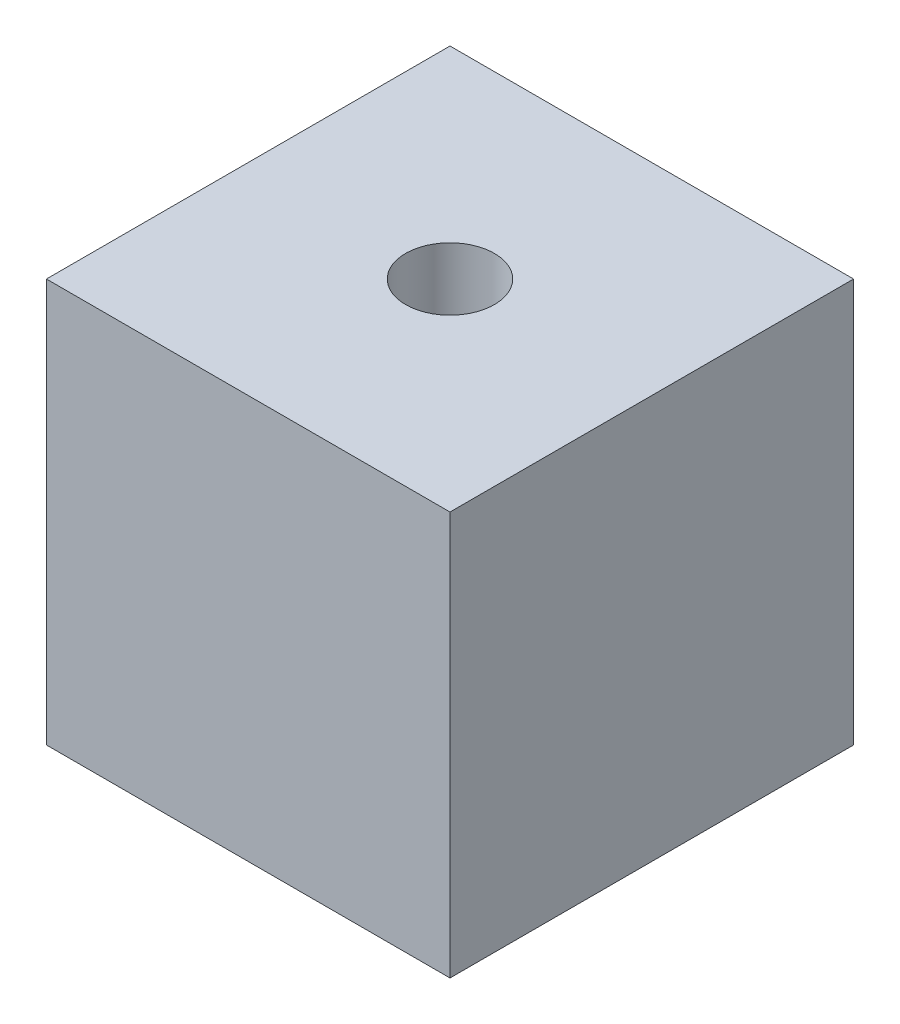
SolidWorks part; units mm, degrees
ref_plane "Front Plane" through (0, 0, 0) normal (0, 0, 1) x (1, 0, 0)
ref_plane "Top Plane" through (0, 0, 0) normal (0, 1, 0) x (1, 0, 0)
ref_plane "Right Plane" through (0, 0, 0) normal (1, 0, 0) x (0, 0, -1)
sketch "Sketch1" plane through (0, 0, 0) normal (0, 1, 0) x (1, 0, 0)
  line L1 (0, 0) -> (10, 0)
  line L2 (0, 0) -> (0, 10)
  line L3 (0, 10) -> (10, 10)
  line L4 (10, 0) -> (10, 10)
  dimension "D1" = 10
  dimension "D2" = 10
extrude "Boss-Extrude1" add sketch "Sketch1" along normal blind 10
hole_wizard "M2 Clearance Hole1" positions "Sketch2" profile "Sketch3" hole size "M2" standard "ISO"
sketch "Sketch2" plane through (0, 10, 0) normal (0, 1, 0) x (1, 0, 0)
  line L0 (10, 10) -> (0, 10) construction
  line L1 (10, 0) -> (10, 10) construction
  point P0 (5, 5)
  dimension "D1" = 5
  dimension "D2" = 5
sketch "Sketch3" plane through (5, 10, -5) normal (1, 0, 0) x (0, 0, 1)
  line L0 (0, 0) -> (0, 8)
  line L1 (0, 8) -> (1.1, 7.3391)
  line L2 (1.1, 7.3391) -> (1.1, 0)
  line L5 (1.1, 0) -> (0, 0)
  line L10 (0, 8) -> (-1.1, 7.3391) construction
  line L11 (0, -6.35) -> (0, 107.95) construction
  dimension "Hole Dia." = 2.2
  dimension "Hole Depth" = 8
  dimension "Drill Angle" = 118
